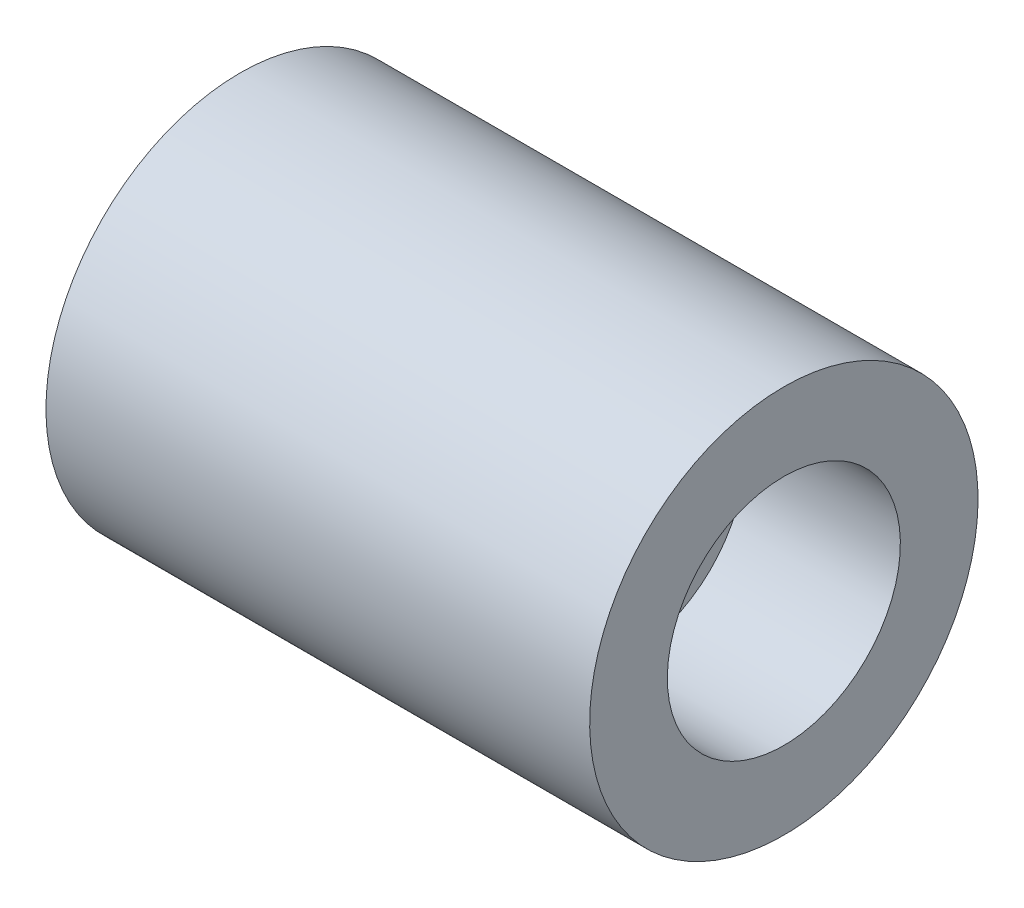
SolidWorks part; units mm, degrees
ref_plane "Alzado" through (0, 0, 0) normal (0, 0, 1) x (1, 0, 0)
ref_plane "Planta" through (0, 0, 0) normal (0, 1, 0) x (1, 0, 0)
ref_plane "Vista lateral" through (0, 0, 0) normal (1, 0, 0) x (0, 0, -1)
sketch "Croquis1" plane through (0, 0, 0) normal (0, 0, 1) x (1, 0, 0)
  line L0 (0, 0) -> (140, 0)
  line L1 (140, 0) -> (140, -20)
  line L2 (140, -20) -> (100, -20)
  line L3 (100, -20) -> (100, -40)
  line L4 (100, -40) -> (20, -40)
  line L5 (20, -40) -> (20, -50)
  line L6 (20, -50) -> (0, -50)
  line L7 (0, -50) -> (0, 0)
  dimension "D1" = 10
  dimension "D2" = 30
  dimension "D3" = 50
  dimension "D4" = 140
  dimension "D5" = 40
  dimension "D6" = 120
revolve "Revolución1" add sketch "Croquis1" angle 360 about L6
equation "\"A\" = 10mm"
equation "\"B\" = 20mm"
equation "\"C\" = 30mm"
equation "\"D1@Croquis1\"=\"A\""
equation "\"D2@Croquis1\"=\"A\"+\"B\""
equation "\"D3@Croquis1\"=\"B\"+\"C\""
equation "\"D4@Croquis1\"=(\"A\"+\"B\"+\"C\"+\"A\")*2"
equation "\"D5@Croquis1\"=\"B\"*2"
equation "\"D6@Croquis1\"=(\"A\"+\"B\"+\"C\")*2"
